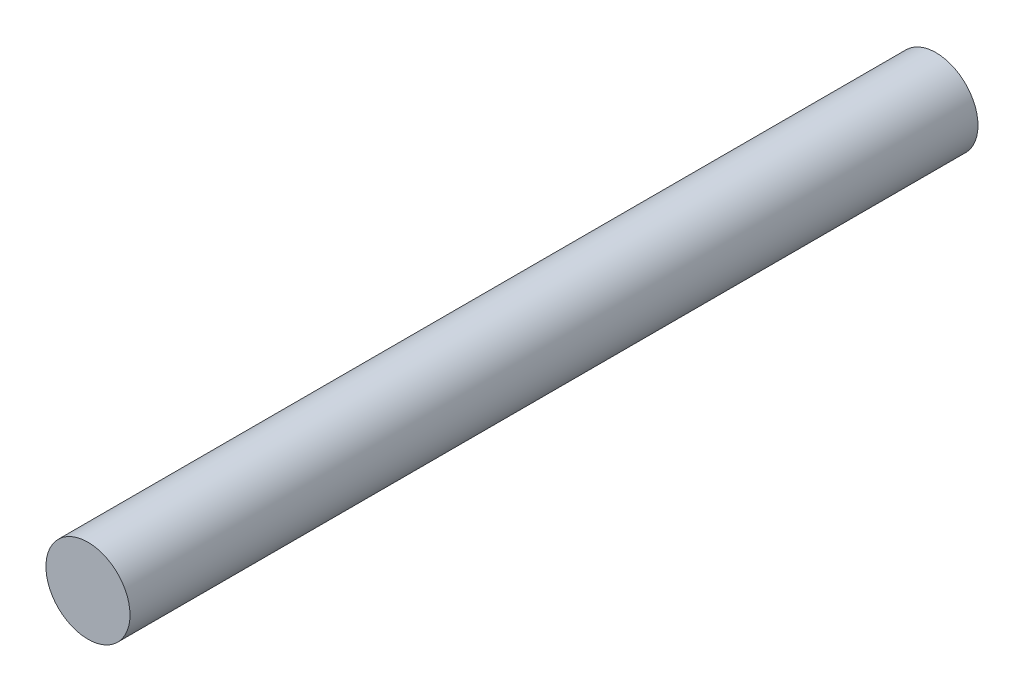
SolidWorks part; units mm, degrees
ref_plane "Ebene vorne" through (0, 0, 0) normal (0, 0, 1) x (1, 0, 0)
ref_plane "Ebene oben" through (0, 0, 0) normal (0, 1, 0) x (1, 0, 0)
ref_plane "Ebene rechts" through (0, 0, 0) normal (1, 0, 0) x (0, 0, -1)
sketch "Skizze1" plane through (0, 0, 0) normal (0, 0, 1) x (1, 0, 0)
  circle A0 centre (0, 0) radius 6
  dimension "D1" = 12
extrude "Aufsatz-Linear austragen1" add sketch "Skizze1" along normal blind 121
